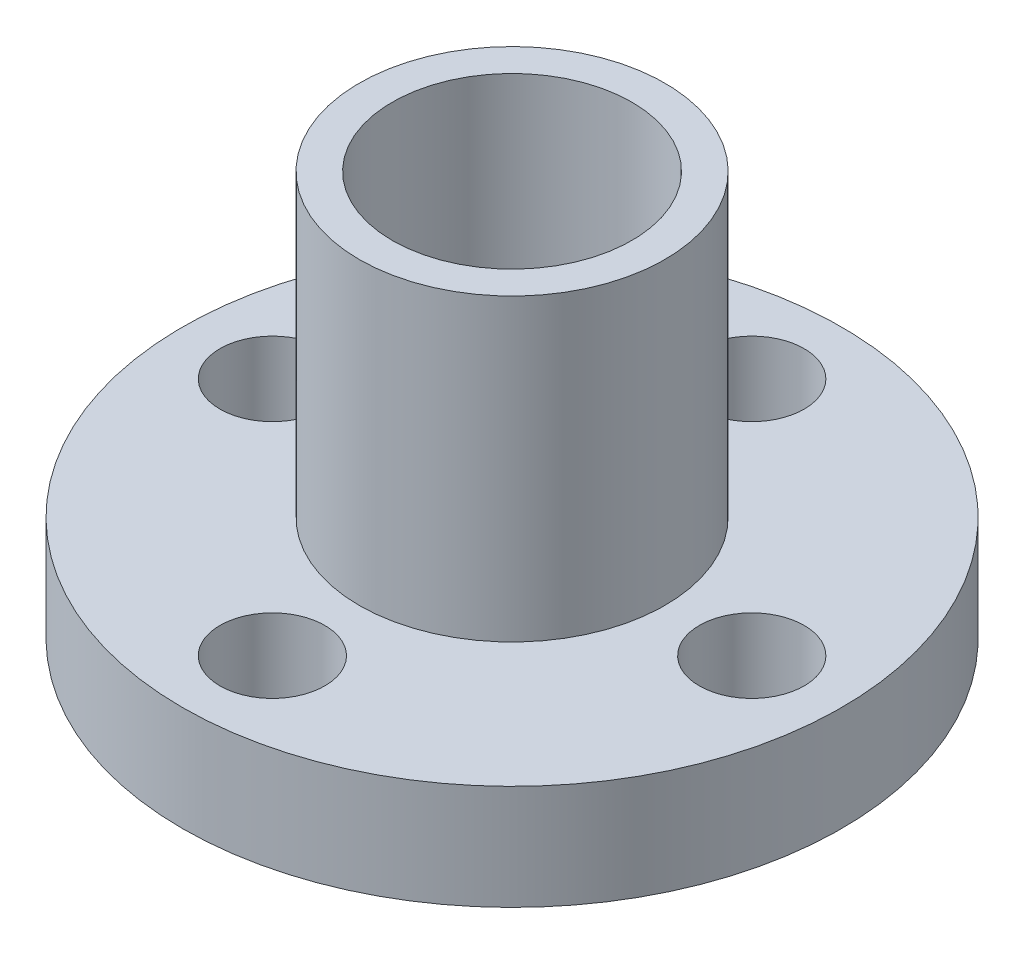
SolidWorks part; units mm, degrees
ref_plane "Front Plane" through (0, 0, 0) normal (0, 0, 1) x (1, 0, 0)
ref_plane "Top Plane" through (0, 0, 0) normal (0, 1, 0) x (1, 0, 0)
ref_plane "Right Plane" through (0, 0, 0) normal (1, 0, 0) x (0, 0, -1)
sketch "Sketch1" plane through (0, 0, 0) normal (0, 1, 0) x (1, 0, 0)
  circle A0 centre (0, 0) radius 5.1
  dimension "D1" = 10.2
extrude "Boss-Extrude1" add sketch "Sketch1" along normal blind 1.5
sketch "Sketch2" plane through (0, 1.5, 0) normal (0, 1, 0) x (1, 0, 0)
  circle A0 centre (0, 0) radius 11
  dimension "D1" = 22
extrude "Boss-Extrude2" add sketch "Sketch2" along normal blind 3.5
sketch "Sketch3" plane through (0, 5, 0) normal (0, 1, 0) x (1, 0, 0)
  circle A0 centre (0, 0) radius 5.1
  dimension "D1" = 10.2
extrude "Boss-Extrude3" add sketch "Sketch3" along normal blind 10
sketch "Sketch4" plane through (0, 15, 0) normal (0, 1, 0) x (1, 0, 0)
  circle A0 centre (0, 0) radius 4
  circle A1 centre (0, 0) radius 8 construction
  circle A2 centre (8, 0) radius 1.75
  circle A3 centre (0, 8) radius 1.75
  circle A4 centre (-8, 0) radius 1.75
  circle A5 centre (0, -8) radius 1.75
  dimension "D1" = 8
  dimension "D2" = 16
  dimension "D3" = 3.5
  dimension "D4" = 3.5
  dimension "D5" = 3.5
  dimension "D6" = 3.5
extrude "Cut-Extrude1" cut sketch "Sketch4" against normal through all
